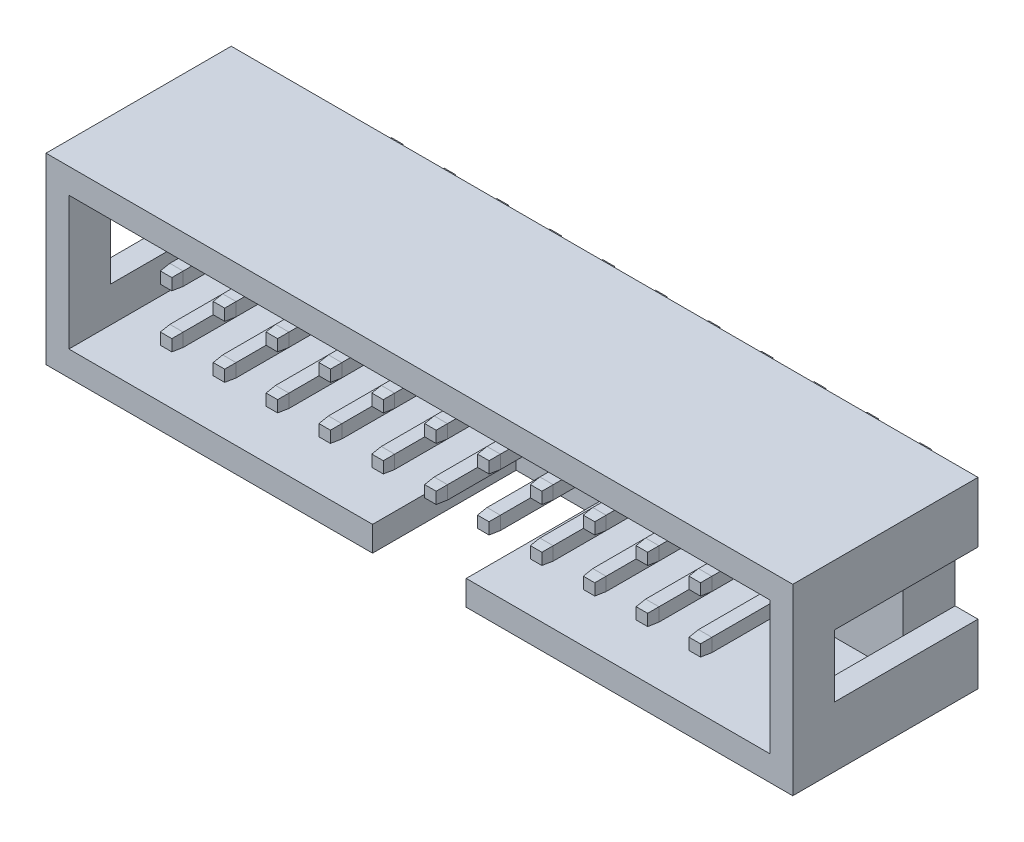
SolidWorks part; units mm, degrees
ref_plane "Front Plane" through (0, 0, 0) normal (0, 0, 1) x (1, 0, 0)
ref_plane "Top Plane" through (0, 0, 0) normal (0, 1, 0) x (1, 0, 0)
ref_plane "Right Plane" through (0, 0, 0) normal (1, 0, 0) x (0, 0, -1)
sketch "Sketch1" plane through (0, 0, 0) normal (0, 0, 1) x (1, 0, 0)
  line L1 (-26.8098, 4.6702) -> (9.0702, 4.6702)
  line L2 (-26.8098, 4.6702) -> (-26.8098, -4.1298)
  line L3 (-26.8098, -4.1298) -> (9.0702, -4.1298)
  line L4 (9.0702, 4.6702) -> (9.0702, -4.1298)
  dimension "D1" = 8.8
  dimension "D2" = 35.88
extrude "Boss-Extrude1" add sketch "Sketch1" along normal blind 2.5
sketch "Sketch2" plane through (0, 0, 2.5) normal (0, 0, 1) x (1, 0, 0)
  line L0 (-26.8098, 0.2702) -> (9.0702, 0.2702) construction
  line L1 (-26.8098, 4.6702) -> (9.0702, 4.6702)
  line L2 (-26.8098, 4.6702) -> (-26.8098, -4.1298)
  line L3 (-26.8098, -4.1298) -> (9.0702, -4.1298)
  line L4 (9.0702, 4.6702) -> (9.0702, -4.1298)
  line L6 (-25.7098, 3.4702) -> (7.9702, 3.4702)
  line L7 (-25.7098, 3.4702) -> (-25.7098, -2.9298)
  line L8 (-25.7098, -2.9298) -> (7.9702, -2.9298)
  line L9 (7.9702, 3.4702) -> (7.9702, -2.9298)
  line L10 (-25.7098, 3.4702) -> (7.9702, -2.9298) construction
  line L11 (-25.7098, -2.9298) -> (7.9702, 3.4702) construction
  point P8 (-8.8698, 0.2702)
  dimension "D1" = 1.1
  dimension "D2" = 1.2
extrude "Boss-Extrude2" add sketch "Sketch2" along normal blind 6.4
sketch "Sketch4" plane through (0, 0, 8.9) normal (0, 0, 1) x (1, 0, 0)
  line L0 (-26.8098, -4.1298) -> (9.0702, -4.1298) construction
  line L1 (-25.7098, -2.9298) -> (7.9702, -2.9298) construction
  line L2 (-11.1198, -2.9298) -> (-6.6198, -2.9298)
  line L3 (-11.1198, -2.9298) -> (-11.1198, -4.1298)
  line L4 (-11.1198, -4.1298) -> (-6.6198, -4.1298)
  line L5 (-6.6198, -2.9298) -> (-6.6198, -4.1298)
  point P10 (-8.8698, -4.1298)
  point P11 (-8.8698, -2.9298)
  point P12 (-6.6198, -3.5298)
  dimension "D1" = 4.5
extrude "Cut-Extrude1" cut sketch "Sketch4" against normal blind 6.9
sketch "Sketch5" plane through (0, 0, 0) normal (0, 0, -1) x (-1, 0, 0)
  line L0 (26.8098, 4.6702) -> (26.8098, -4.1298) construction
  line L1 (26.8098, 1.7702) -> (25.7098, 1.7702)
  line L2 (26.8098, 1.7702) -> (26.8098, -1.2298)
  line L3 (26.8098, -1.2298) -> (25.7098, -1.2298)
  line L4 (25.7098, 1.7702) -> (25.7098, -1.2298)
  line L5 (26.8098, 4.6702) -> (26.8098, -4.1298) construction
  line L6 (-9.0702, 4.6702) -> (-9.0702, -4.1298) construction
  line L8 (-9.0702, 1.7702) -> (-7.9702, 1.7702)
  line L9 (-9.0702, 1.7702) -> (-9.0702, -1.2298)
  line L10 (-9.0702, -1.2298) -> (-7.9702, -1.2298)
  line L11 (-7.9702, 1.7702) -> (-7.9702, -1.2298)
  point P8 (26.8098, 0.2702)
  point P9 (25.7098, 0.2702)
  point P20 (-9.0702, 0.2702)
  point P21 (-7.9702, 0.2702)
  dimension "D1" = 1.1
  dimension "D2" = 3
  dimension "D3" = 1.1
  dimension "D4" = 3
extrude "Cut-Extrude2" cut sketch "Sketch5" against normal blind 6.9
sketch "Sketch6" plane through (0, 0, 2.5) normal (0, 0, 1) x (1, 0, 0)
  line L0 (-26.8098, 4.6702) -> (-26.8098, -4.1298) construction
  line L1 (-22.0598, 1.8602) -> (-21.4198, 1.8602)
  line L2 (-22.0598, 1.8602) -> (-22.0598, 1.2202)
  line L3 (-22.0598, 1.2202) -> (-21.4198, 1.2202)
  line L4 (-21.4198, 1.8602) -> (-21.4198, 1.2202)
  line L5 (-22.0598, 1.8602) -> (-21.4198, 1.2202) construction
  line L6 (-22.0598, 1.2202) -> (-21.4198, 1.8602) construction
  line L7 (-21.7398, 1.5402) -> (-21.7398, -0.9998) construction
  line L8 (-22.0598, -0.6798) -> (-21.4198, -0.6798)
  line L9 (-22.0598, -0.6798) -> (-22.0598, -1.3198)
  line L10 (-22.0598, -1.3198) -> (-21.4198, -1.3198)
  line L11 (-21.4198, -0.6798) -> (-21.4198, -1.3198)
  line L12 (-22.0598, -0.6798) -> (-21.4198, -1.3198) construction
  line L13 (-22.0598, -1.3198) -> (-21.4198, -0.6798) construction
  line L16 (-25.7098, 1.7702) -> (-25.7098, -1.2298) construction
  point P0 (-21.7398, 1.5402)
  point P7 (-21.7398, -0.9998)
  point P12 (-21.7398, 0.2702)
  point P17 (-25.7098, 0.2702)
  dimension "D1" = 0.64
  dimension "D2" = 0.64
  dimension "D3" = 5.07
  dimension "D4" = 0.64
  dimension "D5" = 0.64
  dimension "D6" = 2.54
extrude "Boss-Extrude4" add sketch "Sketch6" along normal blind 5.7 and the other way blind 5.4
chamfer "Chamfer1" distance 0.5 angle 5 4 edges at (-21.7398, 1.8602, 8.2) (-21.4198, 1.5402, 8.2) (-21.7398, 1.2202, 8.2) (-22.0598, 1.5402, 8.2)
chamfer "Chamfer2" distance 0.5 angle 5 4 edges at (-21.7398, -0.6798, 8.2) (-21.4198, -0.9998, 8.2) (-21.7398, -1.3198, 8.2) (-22.0598, -0.9998, 8.2)
chamfer "Chamfer4" distance 0.5 angle 5 4 edges at (-21.7398, 1.8602, -2.9) (-22.0598, 1.5402, -2.9) (-21.7398, 1.2202, -2.9) (-21.4198, 1.5402, -2.9)
chamfer "Chamfer5" distance 0.5 angle 5 4 edges at (-21.7398, -0.6798, -2.9) (-22.0598, -0.9998, -2.9) (-21.7398, -1.3198, -2.9) (-21.4198, -0.9998, -2.9)
pattern_linear "LPattern1" count 11 spacing 2.54 along (1, 0, 0) of "Boss-Extrude4", "Chamfer1", "Chamfer2", "Chamfer4", "Chamfer5"
sketch "Sketch7" plane through (0, 0, -2.9) normal (0, 0, -1) x (-1, 0, 0)
  line L0 (1.6961, 1.2639) -> (1.1436, 1.8164) construction
  line L1 (1.6961, 1.8164) -> (1.1436, 1.2639) construction
  point P8 (1.4198, 1.5402)
ref_plane "Plane1" through (-1.4198, 0, 0) normal (1, 0, 0) x (0, 0, -1)
sketch "Sketch8" plane through (-1.4198, 0, 0) normal (1, 0, 0) x (0, 0, -1)
  line L0 (2.9, 1.5402) -> (6.7616, 1.5402) construction
equation "\"Pitch\"= 2.54"
equation "\"NOC\" = 12"
equation "\"D2@Sketch1\"=\"Pitch\" * \"NOC\" + 5.4"
equation "\"D1@LPattern1\"=\"NOC\" - 1"
